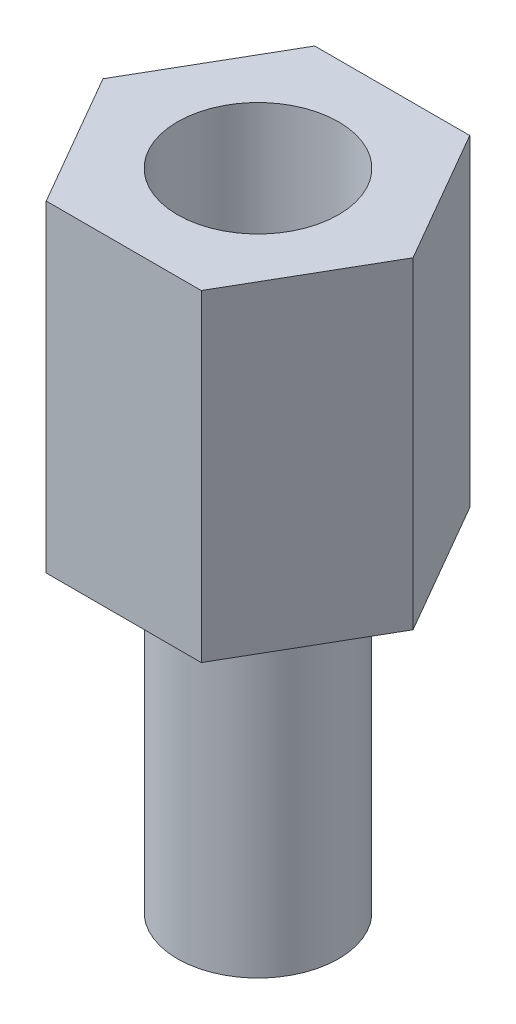
SolidWorks part; units mm, degrees
material "ABS"
ref_plane "Alzado" through (0, 0, 0) normal (0, 0, 1) x (1, 0, 0)
ref_plane "Planta" through (0, 0, 0) normal (0, 1, 0) x (1, 0, 0)
ref_plane "Vista lateral" through (0, 0, 0) normal (1, 0, 0) x (0, 0, -1)
sketch "Croquis1" plane through (0, 0, 0) normal (0, 1, 0) x (1, 0, 0)
  line L1 (1.4434, -2.5) -> (2.8868, 0)
  line L2 (2.8868, 0) -> (1.4434, 2.5)
  line L3 (1.4434, 2.5) -> (-1.4434, 2.5)
  line L4 (-1.4434, 2.5) -> (-2.8868, 0)
  line L5 (-2.8868, 0) -> (-1.4434, -2.5)
  line L6 (-1.4434, -2.5) -> (1.4434, -2.5)
  circle A0 centre (0, 0) radius 2.5 construction
  circle A1 centre (0, 0) radius 1.5
  dimension "D2" = 3
  dimension "D1" = 5
extrude "Saliente-Extruir1" add sketch "Croquis1" along normal blind 6
sketch "Croquis2" plane through (0, 0, 0) normal (0, -1, 0) x (1, 0, 0)
  circle A0 centre (0, 0) radius 1.5 construction
  circle A1 centre (0, 0) radius 1.5
extrude "Saliente-Extruir2" add sketch "Croquis2" along normal blind 6 separate body
